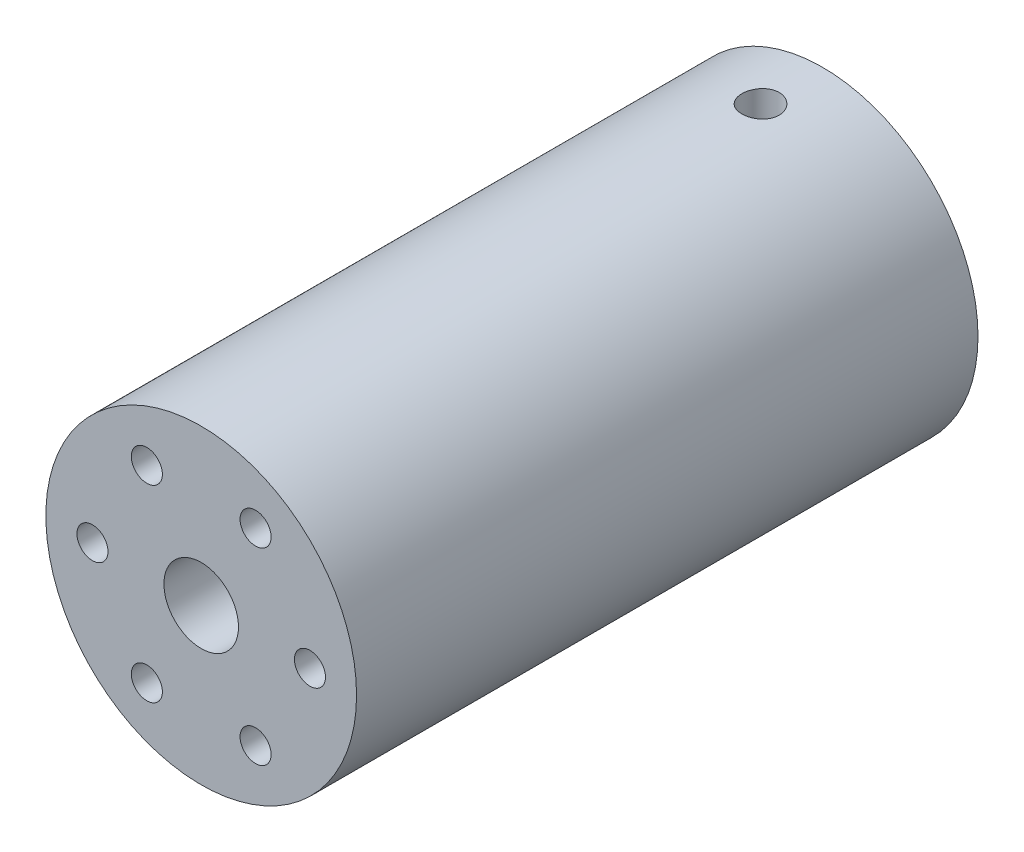
SolidWorks part; units mm, degrees
ref_plane "Alzado" through (0, 0, 0) normal (0, 0, 1) x (1, 0, 0)
ref_plane "Planta" through (0, 0, 0) normal (0, 1, 0) x (1, 0, 0)
ref_plane "Vista lateral" through (0, 0, 0) normal (1, 0, 0) x (0, 0, -1)
sketch "Croquis1" plane through (0, 0, 0) normal (0, 0, 1) x (1, 0, 0)
  circle A0 centre (0, 0) radius 12.5
extrude "Saliente-Extruir1" add sketch "Croquis1" along normal blind 50
sketch "Croquis3" plane through (0, 0, 50) normal (0, 0, 1) x (1, 0, 0)
  line L0 (0, 0) -> (8.75, 0) construction
  circle A0 centre (8.75, 0) radius 1.25
  circle A1 centre (4.375, -7.5777) radius 1.25
  circle A2 centre (-4.375, -7.5777) radius 1.25
  circle A3 centre (-8.75, 0) radius 1.25
  circle A4 centre (-4.375, 7.5777) radius 1.25
  circle A5 centre (4.375, 7.5777) radius 1.25
  circle A6 centre (0, 0) radius 3
  point P17 (0, 0)
  dimension "D1" = 6
extrude "Cortar-Extruir1" cut sketch "Croquis3" against normal through all
sketch "Croquis4" plane through (0, 0, 0) normal (0, 0, -1) x (-1, 0, 0)
  line L0 (0, 0) -> (0, 12.5) construction
  line L2 (-30, 12.5) -> (30, 12.5) construction
  circle A0 centre (0, 0) radius 12.5 construction
  point P9 (0, 12.5)
sketch3d "Croquis3D2"
  line L0 (30, 12.5, 0) -> (-30, 12.5, 0) construction
sketch "Croquis6" plane through (0, 12.5, 0) normal (0, 1, 0) x (1, 0, 0)
  line L0 (0, 0) -> (0, -5) construction
  circle A0 centre (0, -5) radius 1.5
extrude "Cortar-Extruir2" cut sketch "Croquis6" against normal through all
